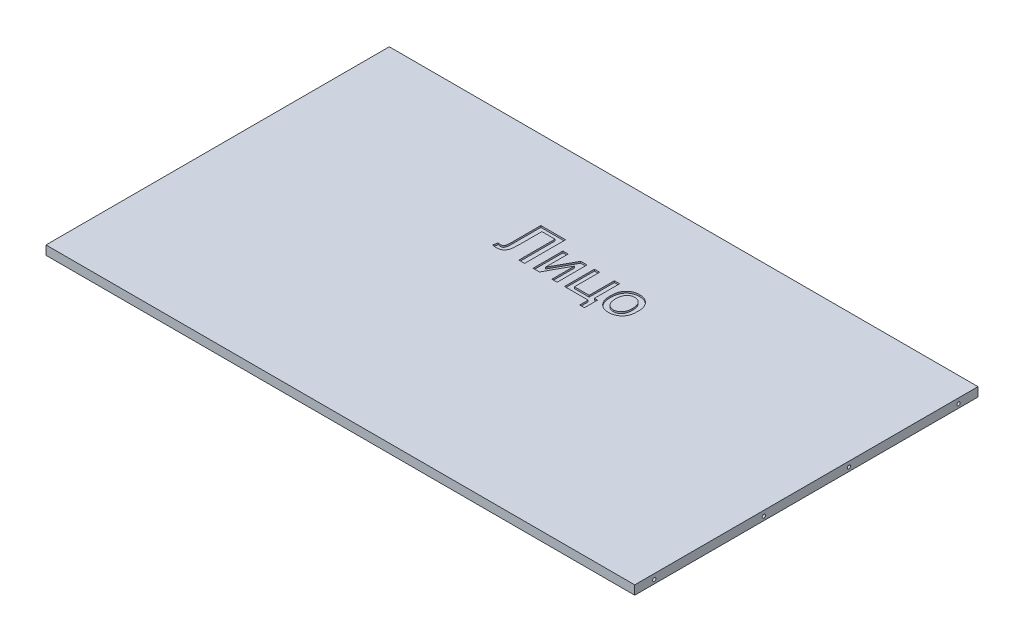
SolidWorks part; units mm, degrees
ref_plane "Спереди" through (0, 0, 0) normal (0, 0, 1) x (1, 0, 0)
ref_plane "Сверху" through (0, 0, 0) normal (0, 1, 0) x (1, 0, 0)
ref_plane "Справа" through (0, 0, 0) normal (1, 0, 0) x (0, 0, -1)
sketch "Эскиз1" plane through (0, 0, 0) normal (0, 1, 0) x (1, 0, 0)
  line L0 (0, 0) -> (-111408.4852, 0) construction
  line L1 (0, 0) -> (0, -111408.4852) construction
  line L3 (179.65, 104.75) -> (-179.65, 104.75)
  line L4 (179.65, 104.75) -> (179.65, -104.75)
  line L5 (179.65, -104.75) -> (-179.65, -104.75)
  line L6 (-179.65, 104.75) -> (-179.65, -104.75)
  line L7 (179.65, 104.75) -> (-179.65, -104.75) construction
  line L8 (179.65, -104.75) -> (-179.65, 104.75) construction
  point P5 (0, 0)
  dimension "D1" = 359.3
  dimension "D2" = 209.5
extrude "Бобышка-Вытянуть1" add sketch "Эскиз1" along normal blind 5.5
sketch "Эскиз2" plane through (0, 5.5, 0) normal (0, 1, 0) x (1, 0, 0)
  text T0 "Лицо" font "Arial" height 25
extrude "Вырез-Вытянуть1" cut sketch "Эскиз2" against normal blind 1
sketch "Эскиз3" plane through (-179.65, 0, 0) normal (-1, 0, 0) x (0, 0, 1)
  line L0 (91.968, 2.4) -> (-49908.032, 3.2378) construction
  line L1 (-104.75, 5.5) -> (104.75, 5.5) construction
  line L3 (104.75, 5.5) -> (104.75, 0) construction
  circle A0 centre (92.85, 2.4) radius 1
  circle A1 centre (25.95, 2.4011) radius 1
  circle A2 centre (-25.95, 2.402) radius 1
  circle A3 centre (-92.85, 2.4031) radius 1
  point P8 (46.3977, 2.5764)
  point P10 (-13.4604, 2.5774)
  point P15 (104.75, 1.4007)
  dimension "D1" = 2
  dimension "D2" = 3.1
  dimension "D3" = 11.9
  dimension "D4" = 66.9
  dimension "D5" = 118.8
  dimension "D6" = 185.7
extrude "Вырез-Вытянуть2" cut sketch "Эскиз3" against normal blind 2.5
mirror "Зеркальное отражение1" about plane through (0, 0, 0) normal (1, 0, 0) of "Вырез-Вытянуть2"
